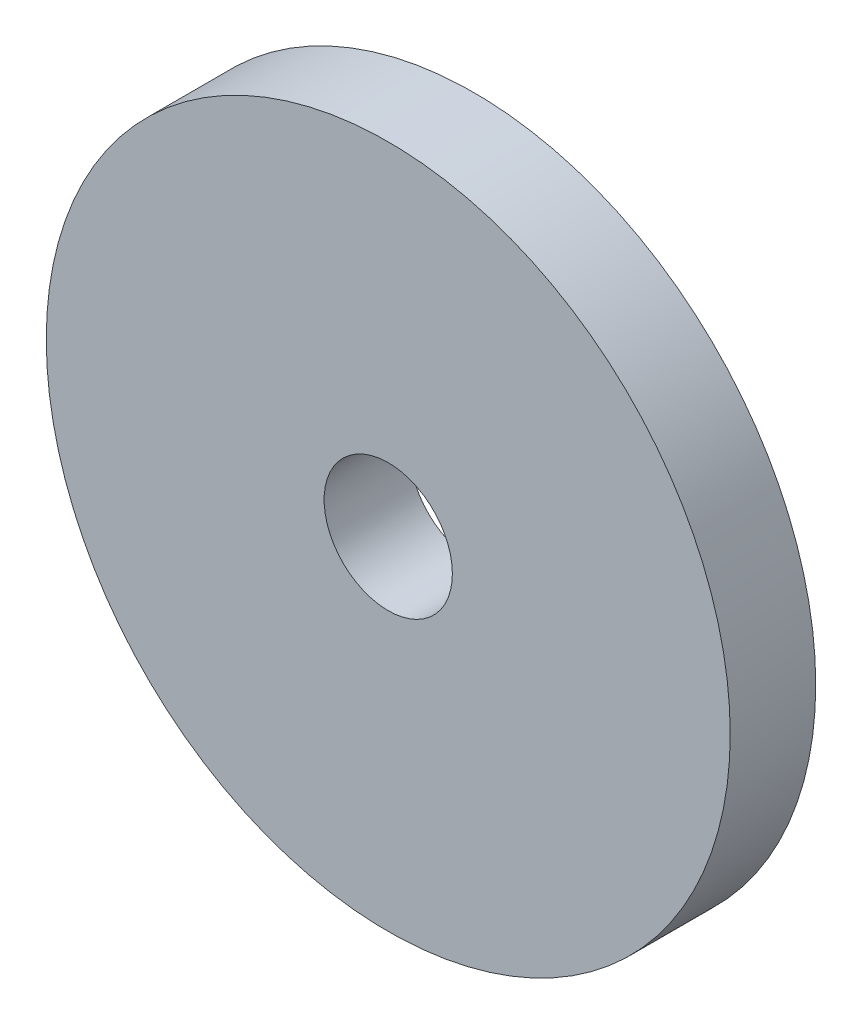
SolidWorks part; units mm, degrees
ref_plane "Front Plane" through (0, 0, 0) normal (0, 0, 1) x (1, 0, 0)
ref_plane "Top Plane" through (0, 0, 0) normal (0, 1, 0) x (1, 0, 0)
ref_plane "Right Plane" through (0, 0, 0) normal (1, 0, 0) x (0, 0, -1)
sketch "Sketch1" plane through (0, 0, 0) normal (0, 0, 1) x (1, 0, 0)
  circle A0 centre (0, 0) radius 8
  circle A1 centre (0, 0) radius 1.5
  dimension "D1" = 16
  dimension "D2" = 3
extrude "Boss-Extrude1" add sketch "Sketch1" along normal blind 2
